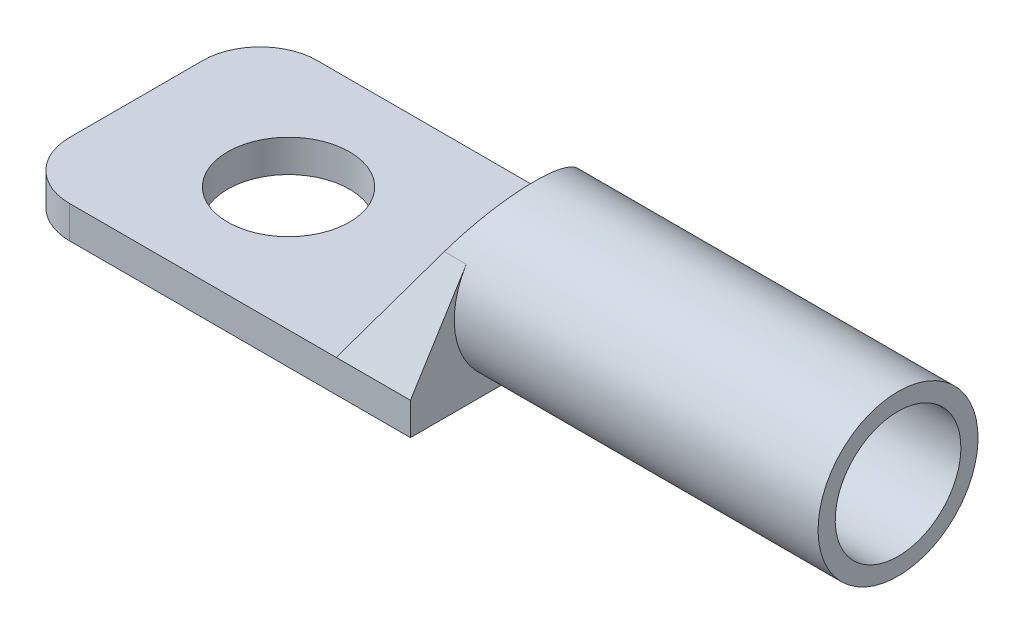
SolidWorks part; units mm, degrees
ref_plane "Alzado" through (0, 0, 0) normal (0, 0, 1) x (1, 0, 0)
ref_plane "Planta" through (0, 0, 0) normal (0, 1, 0) x (1, 0, 0)
ref_plane "Vista lateral" through (0, 0, 0) normal (1, 0, 0) x (0, 0, -1)
sketch "Croquis1" plane through (0, 0, 0) normal (0, 0, 1) x (1, 0, 0)
  line L0 (0, 0) -> (0, 13)
  line L1 (0, 13) -> (40, 13)
  line L2 (40, 13) -> (40, 0)
  line L3 (40, 0) -> (0, 0)
  dimension "D1" = 40
  dimension "D2" = 13
extrude "Saliente-Extruir1" add sketch "Croquis1" along normal blind 13
sketch "Croquis2" plane through (40, 0, 0) normal (1, 0, 0) x (0, 0, -1)
  circle A0 centre (-6.5, 6.5) radius 3.3
  dimension "D1" = 6.6
extrude "Cortar-Extruir1" cut sketch "Croquis2" against normal blind 17
sketch "Croquis3" plane through (0, 13, 0) normal (0, 1, 0) x (1, 0, 0)
  line L1 (0, -13) -> (0, 0) construction
  line L2 (8, -6.5) -> (17, -6.5) construction
  circle A0 centre (8, -6.5) radius 3.2
  dimension "D1" = 6.4
  dimension "D2" = 8
  dimension "D3" = 9
extrude "Cortar-Extruir4" cut sketch "Croquis3" against normal blind 19
sketch "Croquis7" plane through (0, 13, 0) normal (0, 1, 0) x (1, 0, 0)
  line L0 (8, -6.5) -> (17, -6.5) construction
  line L1 (17, -13) -> (17, 0)
  line L2 (40, -13) -> (0, -13) construction
  line L3 (40, 0) -> (0, 0) construction
  line L4 (17, -13) -> (0, -13)
  line L5 (0, -13) -> (0, 0)
  line L6 (0, 0) -> (17, 0)
  dimension "D1" = 9
extrude "Cortar-Extruir5" cut sketch "Croquis7" against normal blind 9
sketch "Croquis8" plane through (40, 0, 0) normal (1, 0, 0) x (0, 0, -1)
  circle A0 centre (-6.5, 6.5) radius 4.2
  dimension "D1" = 8.4
extrude "Cortar-Extruir6" cut sketch "Croquis8" against normal blind 19.1 flip side to cut
sketch "Croquis9" plane through (0, 13, 0) normal (0, 1, 0) x (1, 0, 0)
  line L0 (17, 0) -> (20.9, 0)
  line L1 (20.9, 0) -> (20.9, -13)
  line L2 (20.9, -13) -> (17, -13)
  line L3 (17, -13) -> (17, 0) construction
  line L4 (20.9, -13) -> (17, -13) construction
  line L5 (17, -13) -> (17, 0)
extrude "Cortar-Extruir7" cut sketch "Croquis9" against normal blind 2.3
sketch "Croquis10" plane through (0, 0, 0) normal (0, -1, 0) x (1, 0, 0)
  line L0 (0, 13) -> (20.9, 13)
  line L1 (20.9, 13) -> (20.9, 0)
  line L2 (20.9, 0) -> (0, 0)
  line L3 (0, 0) -> (0, 13)
extrude "Cortar-Extruir8" cut sketch "Croquis10" against normal blind 2.3
sketch "Croquis11" plane through (0, 0, 13) normal (0, 0, 1) x (1, 0, 0)
  line L0 (17, 4) -> (17, 10.7)
  line L1 (17, 10.7) -> (20.9, 10.7)
  line L2 (20.9, 10.7) -> (17, 4)
extrude "Cortar-Extruir9" cut sketch "Croquis11" against normal blind 22.3
sketch "Croquis13" plane through (20.9, 0, 0) normal (1, 0, 0) x (0, 0, -1)
  line L0 (-13, 4) -> (-13, 10.7)
  line L1 (-13, 4) -> (-8.8343, 10.7)
  line L2 (-13, 10.7) -> (-6.5, 10.7) construction
  line L3 (-8.8343, 10.7) -> (-13, 10.7)
extrude "Cortar-Extruir10" cut sketch "Croquis13" against normal blind 22.3
sketch "Croquis14" plane through (20.9, 0, 0) normal (1, 0, 0) x (0, 0, -1)
  line L0 (0, 4) -> (0, 10.7)
  line L1 (0, 4) -> (-4.1655, 10.7)
  line L2 (-6.5, 10.7) -> (0, 10.7) construction
  line L3 (-4.1655, 10.7) -> (0, 10.7)
extrude "Cortar-Extruir11" cut sketch "Croquis14" against normal blind 22.3
sketch "Croquis15" plane through (40, 0, 0) normal (1, 0, 0) x (0, 0, -1)
  line L2 (-10.0668, 8.7176) -> (-11.1353, 9.382)
  line L3 (-2.9332, 8.7176) -> (-1.8646, 9.3819)
  arc A0 (-2.9332, 8.7176) -> (-10.0668, 8.7176) centre (-6.5, 6.5) ccw
  arc A2 (-1.8646, 9.3819) -> (-11.1353, 9.382) centre (-6.5, 6.5) ccw
extrude "Cortar-Extruir12" cut sketch "Croquis15" against normal blind 32.3
fillet "Redondeo1" radius 3 2 edges at (0, 3.15, 13) (0, 3.15, 0)
